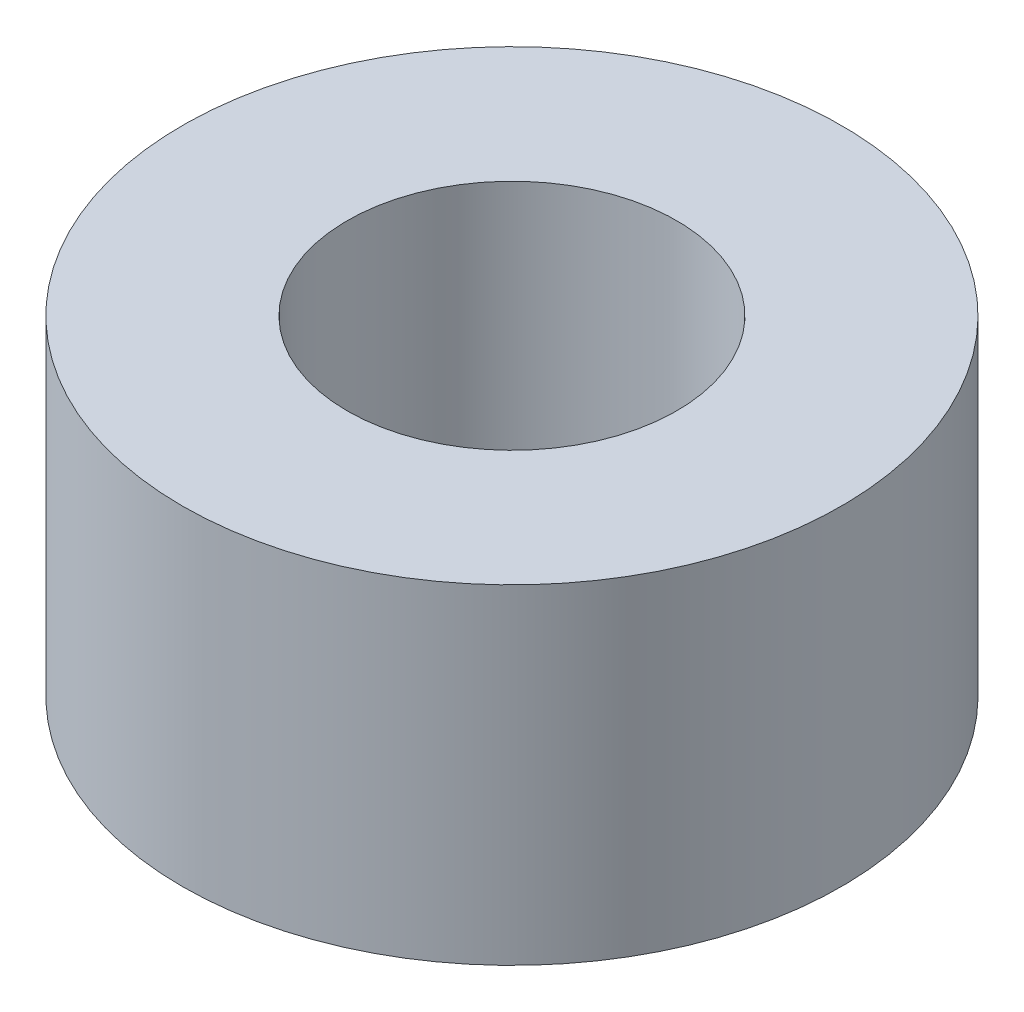
SolidWorks part; units mm, degrees
ref_plane "Alzado" through (0, 0, 0) normal (0, 0, 1) x (1, 0, 0)
ref_plane "Planta" through (0, 0, 0) normal (0, 1, 0) x (1, 0, 0)
ref_plane "Vista lateral" through (0, 0, 0) normal (1, 0, 0) x (0, 0, -1)
sketch "Croquis1" plane through (0, 0, 0) normal (0, 1, 0) x (1, 0, 0)
  circle A0 centre (0, 0) radius 3.175
  circle A1 centre (0, 0) radius 1.5875
  dimension "D1" = 3.175
  dimension "D2" = 6.35
extrude "Saliente-Extruir1" add sketch "Croquis1" along normal blind 3.175
